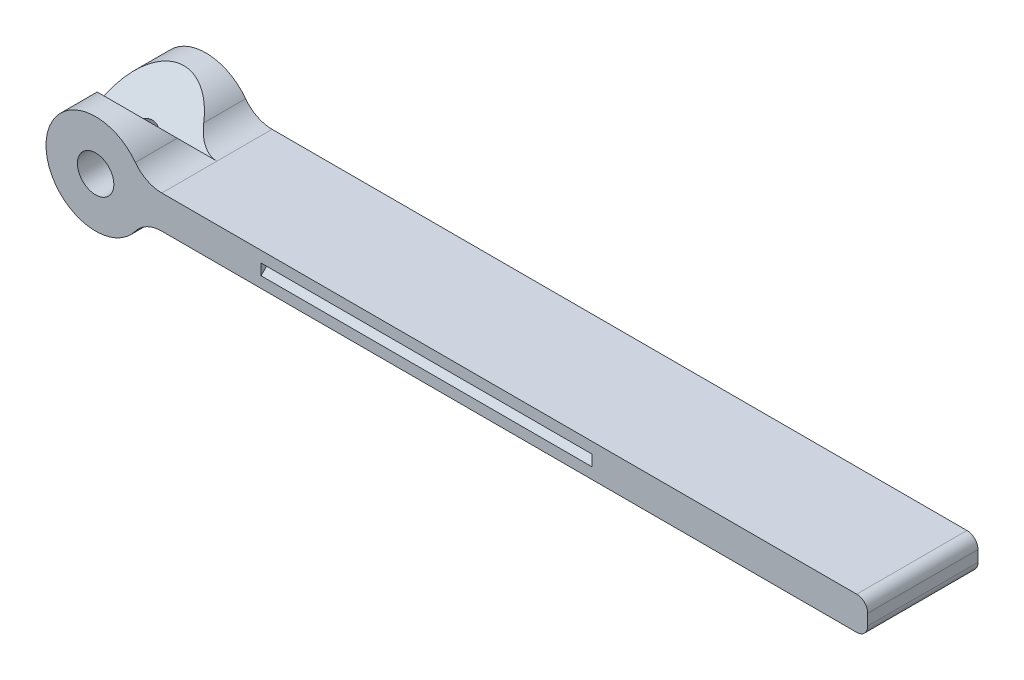
SolidWorks part; units mm, degrees
ref_plane "Front Plane" through (0, 0, 0) normal (0, 0, 1) x (1, 0, 0)
ref_plane "Top Plane" through (0, 0, 0) normal (0, 1, 0) x (1, 0, 0)
ref_plane "Right Plane" through (0, 0, 0) normal (1, 0, 0) x (0, 0, -1)
sketch "Sketch1" plane through (0, 0, 0) normal (0, 0, 1) x (1, 0, 0)
  line L4 (52.0627, 9.1402) -> (-10.9373, 9.1402)
  line L7 (53.0627, 11.1402) -> (53.0627, 10.1402)
  line L8 (-20.03, 10.6402) -> (-16.2061, 10.6402) construction
  line L9 (-10.9373, 12.1402) -> (52.0627, 12.1402)
  circle A11 centre (-16.9373, 10.6402) radius 1.65
  arc A12 (-13.3373, 13.3402) -> (-13.3373, 7.9402) centre (-16.9373, 10.6402) ccw
  arc A13 (-10.9373, 9.1402) -> (-13.3373, 7.9402) centre (-10.9373, 6.1402) ccw
  arc A14 (-10.9373, 12.1402) -> (-13.3373, 13.3402) centre (-10.9373, 15.1402) cw
  arc A15 (52.0627, 9.1402) -> (53.0627, 10.1402) centre (52.0627, 10.1402) ccw
  arc A16 (52.0627, 12.1402) -> (53.0627, 11.1402) centre (52.0627, 11.1402) cw
  point P8 (-19.9739, 5.4687)
  point P11 (-19.9739, 2.4687)
  dimension "D6" = 3.3
  dimension "D7" = 3
  dimension "D8" = 4.5
  dimension "D4" = 1
  dimension "D1" = 1.5
  dimension "D2" = 3
  dimension "D3" = 70
  dimension "D9" = 3
extrude "Boss-Extrude1" add sketch "Sketch1" along normal blind 10
sketch "Sketch7" plane through (0, 0, 0) normal (1, 0, 0) x (0, 0, -1)
  line L0 (-5, 15.1402) -> (-5, 1.3196) construction
  line L1 (0, 15.1402) -> (-10, 15.1402) construction
  line L2 (-8, 15.1402) -> (-5, 12.1402)
  line L3 (-5, 12.1402) -> (-2, 15.1402)
  line L4 (-2, 15.1402) -> (-8, 15.1402)
  line L5 (-10, 12.1402) -> (0, 12.1402) construction
  dimension "D1" = 45
extrude "Cut-Extrude1" cut sketch "Sketch7" against normal blind 29
sketch "Sketch8" plane through (53.0627, 0, 0) normal (1, 0, 0) x (0, 0, -1)
  line L0 (0, 11.1402) -> (-0.5, 10.6402)
  line L1 (-0.5, 10.6402) -> (0, 10.1402)
  line L2 (0, 11.1402) -> (0, 10.1402)
extrude "Cut-Extrude2" cut sketch "Sketch8" against normal blind 30 from offset 25 offset against normal yes
ref_plane "Plane1" through (0, 0, 5) normal (0, 0, -1) x (-1, 0, 0)
mirror "Mirror1" about plane through (0, 0, 5) normal (0, 0, -1) of "Cut-Extrude2"
sketch "Sketch9" plane through (0, 12.1402, 0) normal (0, 1, 0) x (1, 0, 0)
  line L0 (4.95, -5) -> (-4.95, -5) construction
  circle A0 centre (-8.2714, -5) radius 0.75
  circle A1 centre (-2.4034, -5) radius 0.75
  circle A2 centre (3.4645, -5) radius 0.75
  circle A3 centre (9.3325, -5) radius 0.75
  circle A4 centre (15.2005, -5) radius 0.75
  dimension "D1" = 1.5
  dimension "D2" = 5
